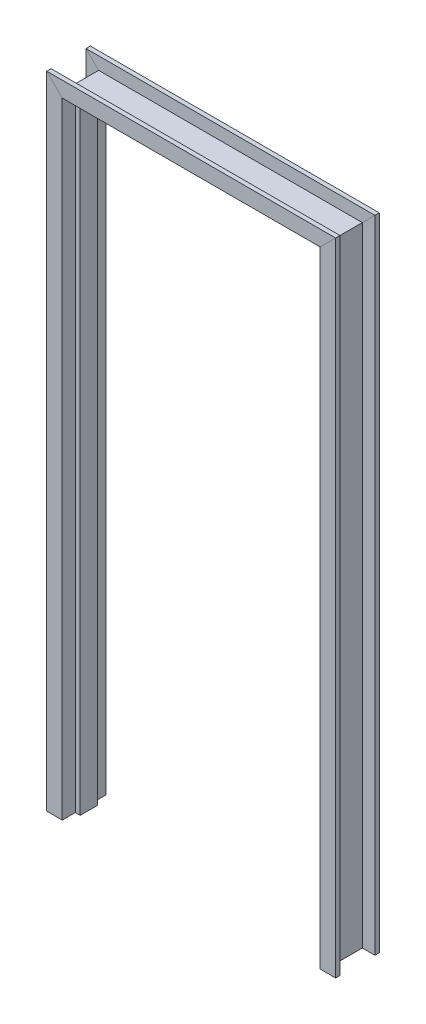
SolidWorks part; units mm, degrees
material "AISI 1020 Steel, Cold Rolled"
ref_plane "Front Plane" through (0, 0, 0) normal (0, 0, 1) x (1, 0, 0)
ref_plane "Top Plane" through (0, 0, 0) normal (0, 1, 0) x (1, 0, 0)
ref_plane "Right Plane" through (0, 0, 0) normal (1, 0, 0) x (0, 0, -1)
sketch "Sketch1" plane through (0, 0, 0) normal (0, 0, 1) x (1, 0, 0)
  line L0 (0, 0) -> (0, 2032)
  line L1 (0, 2032) -> (812.8, 2032)
  line L2 (812.8, 2032) -> (812.8, 0)
  line L3 (447.04, 0) -> (-447.04, 0) construction
  dimension "D1" = 2032
  dimension "D2" = 812.8
  dimension "D3" = 2032
sketch "Sketch2" plane through (0, 0, 0) normal (0, 1, 0) x (1, 0, 0)
  line L0 (0, 0) -> (0, 57.15)
  line L1 (0, 57.15) -> (-15.875, 57.15)
  line L2 (-15.875, 57.15) -> (-15.875, 100.0125)
  line L3 (-15.875, 100.0125) -> (-66.675, 100.0125)
  line L4 (-66.675, 100.0125) -> (-66.675, 85.725)
  line L5 (-66.675, 85.725) -> (-25.4, 85.725)
  line L6 (-25.4, 85.725) -> (-25.4, -28.575)
  line L7 (-25.4, -28.575) -> (-66.675, -28.575)
  line L8 (-66.675, -28.575) -> (-66.675, -42.8625)
  line L9 (-66.675, -42.8625) -> (-15.875, -42.8625)
  line L10 (-15.875, -42.8625) -> (-15.875, 0)
  line L11 (-15.875, 0) -> (0, 0)
  dimension "D1" = 142.875
  dimension "D2" = 114.3
  dimension "D3" = 25.4
  dimension "D4" = 57.15
  dimension "D5" = 15.875
  dimension "D6" = 50.8
  dimension "D7" = 50.8
sweep "Sweep1" add profiles "Sketch2" path "Sketch1"
